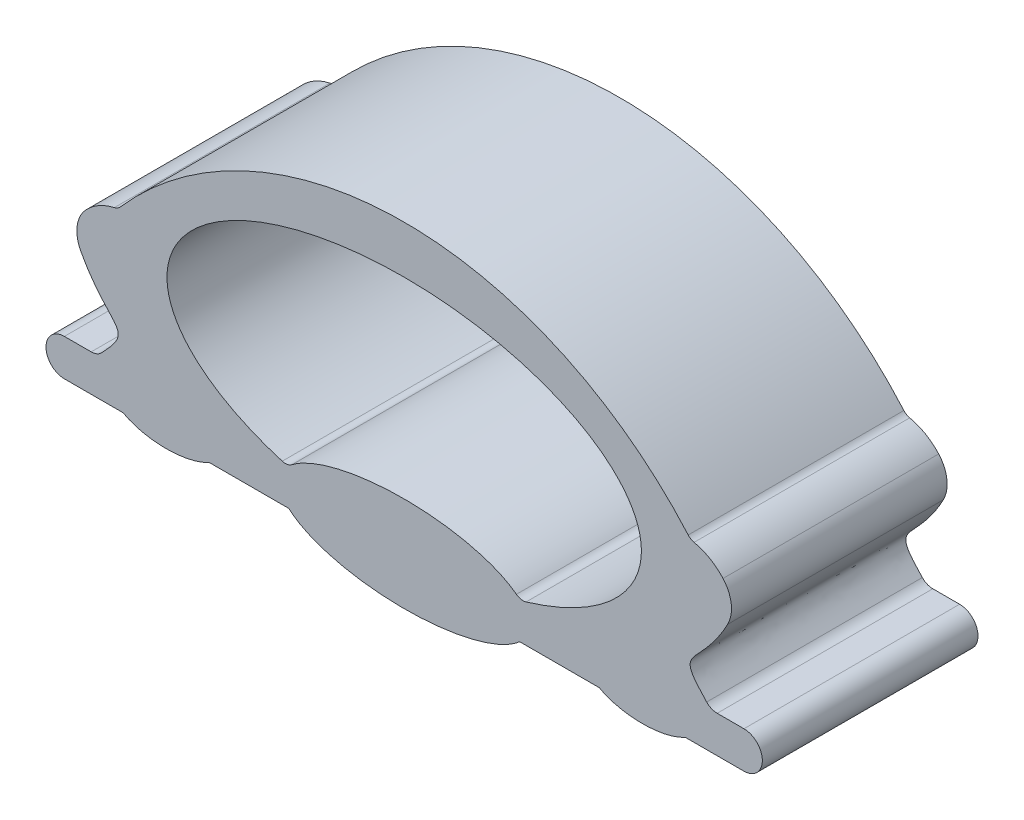
SolidWorks part; units mm, degrees
ref_plane "Alzado" through (0, 0, 0) normal (0, 0, 1) x (1, 0, 0)
ref_plane "Planta" through (0, 0, 0) normal (0, 1, 0) x (1, 0, 0)
ref_plane "Vista lateral" through (0, 0, 0) normal (1, 0, 0) x (0, 0, -1)
sketch "Croquis2" plane through (0, 0, 0) normal (0, 0, 1) x (1, 0, 0)
  line L0 (1.5756, 0.3058) -> (1.4514, 0.3058)
  line L1 (0, -0.9979) -> (0, 1.8615) construction
  line L2 (-1.5756, 0.1352) -> (-1.3036, 0.1352)
  line L3 (-0.9046, 0.1352) -> (-0.5353, 0.1352)
  line L4 (-1.5756, 0.3058) -> (-1.4514, 0.3058)
  line L5 (0.9046, 0.1352) -> (0.5353, 0.1352)
  line L6 (1.5756, 0.1352) -> (1.3036, 0.1352)
  arc A0 (-1.5756, 0.3058) -> (-1.5756, 0.1352) centre (-1.5756, 0.2205) ccw
  arc A1 (-1.5, 0.6873) -> (-1.4786, 0.8608) centre (-1.3653, 0.7588) cw
  arc A2 (-1.4786, 0.8608) -> (-1.3442, 0.9386) centre (-1.2911, 0.6919) cw
  arc A3 (-1.4514, 0.3058) -> (-1.4027, 0.3266) centre (-1.4514, 0.3733) ccw
  arc A4 (1.3171, 0.9546) -> (-1.3171, 0.9546) centre (0, -0.1967) ccw
  arc A9 (-0.5653, 0.3099) -> (-0.5205, 0.3181) centre (-0.551, 0.3578) ccw
  arc A10 (-0.5226, 0.1245) -> (-0.5535, 0.1352) centre (-0.5535, 0.0852) ccw
  arc A11 (-0.8922, 0.1352) -> (-0.9146, 0.1299) centre (-0.8922, 0.0852) ccw
  arc A12 (-1.2935, 0.1299) -> (-1.316, 0.1352) centre (-1.316, 0.0852) ccw
  arc A13 (-1.3442, 0.9386) -> (-1.3171, 0.9546) centre (-1.3548, 0.9875) ccw
  arc A14 (1.3442, 0.9386) -> (1.3171, 0.9546) centre (1.3548, 0.9875) cw
  arc A15 (1.2935, 0.1299) -> (1.316, 0.1352) centre (1.316, 0.0852) cw
  arc A16 (0.8922, 0.1352) -> (0.9146, 0.1299) centre (0.8922, 0.0852) cw
  arc A17 (0.5226, 0.1245) -> (0.5535, 0.1352) centre (0.5535, 0.0852) cw
  arc A18 (0.5653, 0.3099) -> (0.5205, 0.3181) centre (0.551, 0.3578) cw
  arc A19 (1.4514, 0.3058) -> (1.4027, 0.3266) centre (1.4514, 0.3733) cw
  arc A20 (1.4786, 0.8608) -> (1.3442, 0.9386) centre (1.2911, 0.6919) ccw
  arc A21 (1.5, 0.6873) -> (1.4786, 0.8608) centre (1.3653, 0.7588) ccw
  arc A22 (1.5756, 0.3058) -> (1.5756, 0.1352) centre (1.5756, 0.2205) cw
  ellipse E0 centre (1.1041, 0.2205) end of major axis (0.8393, 0.2205) minor radius 0.1297 (1.3036, 0.1352) -> (0.9046, 0.1352) cw
  ellipse E1 centre (0, 0.7817) end of major axis (1.1, 0.7817) minor radius 0.55 (0.5653, 0.3099) -> (-0.5653, 0.3099) ccw
  ellipse E2 centre (0, 0.2205) end of major axis (0.5805, 0.2205) minor radius 0.2205 (-0.5353, 0.1352) -> (0.5353, 0.1352) ccw
  ellipse E3 centre (-1.1041, 0.2205) end of major axis (-0.8393, 0.2205) minor radius 0.1297 (-1.3036, 0.1352) -> (-0.9046, 0.1352) ccw
  ellipse E4 centre (0, 0.2205) end of major axis (0.5805, 0.2205) minor radius 0.2205 (0.5205, 0.3181) -> (-0.5205, 0.3181) ccw
  ellipse E5 centre (0, 0.2205) end of major axis (0.5805, 0.2205) minor radius 0.2205 (-0.5353, 0.1352) -> (0, 0) ccw
  spline S0 degree 3 poles (-1.4027, 0.3266) (-1.3601, 0.3709) (-1.2731, 0.4746) (-1.4058, 0.5099) (-1.5, 0.6873) knots 0.042799 0.042799 0.042799 0.042799 0.330664 1 1 1 1
  spline S1 degree 3 poles (1.4027, 0.3266) (1.3601, 0.3709) (1.2731, 0.4746) (1.4058, 0.5099) (1.5, 0.6873) knots 0.042799 0.042799 0.042799 0.042799 0.330664 1 1 1 1
  point P3 (0, 0)
  point P6 (0, 1.3317)
  point P42 (0, 0.441)
  point P49 (-0.8513, 0.0512)
  point P50 (-0.8524, 0.0852)
  point P52 (-1.3552, 0.0852)
  dimension "D2" = 1.1
  dimension "D4" = 0.1
  dimension "D5" = 0.1
  dimension "D6" = 0.1
  dimension "D7" = 0.1
  dimension "D8" = 0.1
  dimension "D1" = 1.5
  dimension "D3" = 2.2
extrude "Saliente-Extruir2" add sketch "Croquis2" against normal blind 1 contours E2 L1 E4 A9 E1 A4 A13 A2 A1 S0 A3 L4 A0 L2 E3 L3 | L1 E2 L5 E0 L6 A22 L0 A19 S1 A21 A20 A14 A4 E1 A18 E4
